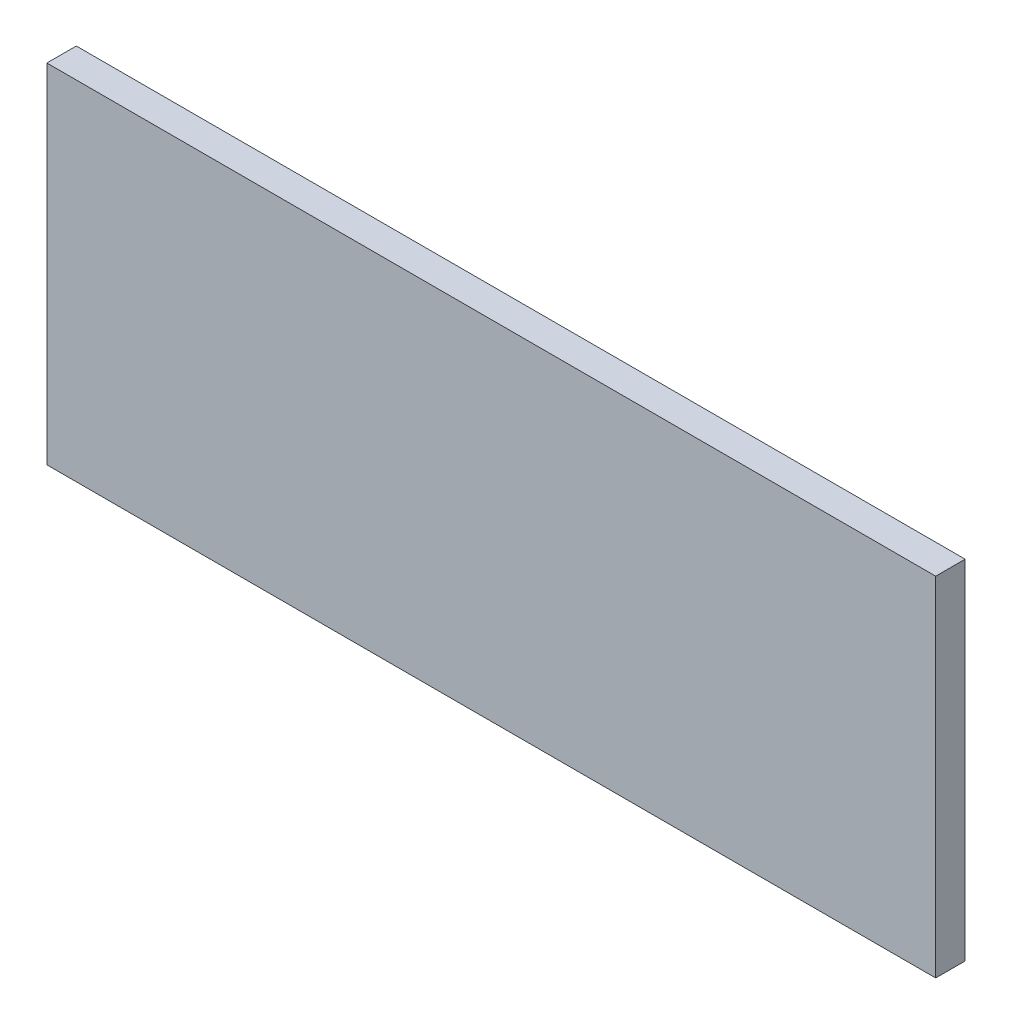
SolidWorks part; units mm, degrees
material "Acrylic (Medium-high impact)"
ref_plane "Front Plane" through (0, 0, 0) normal (0, 0, 1) x (1, 0, 0)
ref_plane "Top Plane" through (0, 0, 0) normal (0, 1, 0) x (1, 0, 0)
ref_plane "Right Plane" through (0, 0, 0) normal (1, 0, 0) x (0, 0, -1)
sketch "Sketch1" plane through (0, 0, 0) normal (0, 0, 1) x (1, 0, 0)
  line L9 (3093.6428, 1138.8097) -> (3070.6348, 1138.8097)
  line L10 (3070.6348, 1138.8097) -> (3070.6348, 1129.8017)
  line L11 (3070.6348, 1129.8017) -> (3093.6428, 1129.8017)
  line L12 (3093.6428, 1129.8017) -> (3093.6428, 1138.8097)
  line L13 (3093.6428, 1138.8097) -> (3070.6348, 1138.8097)
  line L14 (3070.6348, 1138.8097) -> (3070.6348, 1129.8017)
  line L15 (3070.6348, 1129.8017) -> (3093.6428, 1129.8017)
  line L16 (3093.6428, 1129.8017) -> (3093.6428, 1138.8097)
  dimension "D1" = 0.254
extrude "Boss-Extrude1" add sketch "Sketch1" along normal blind 0.762
